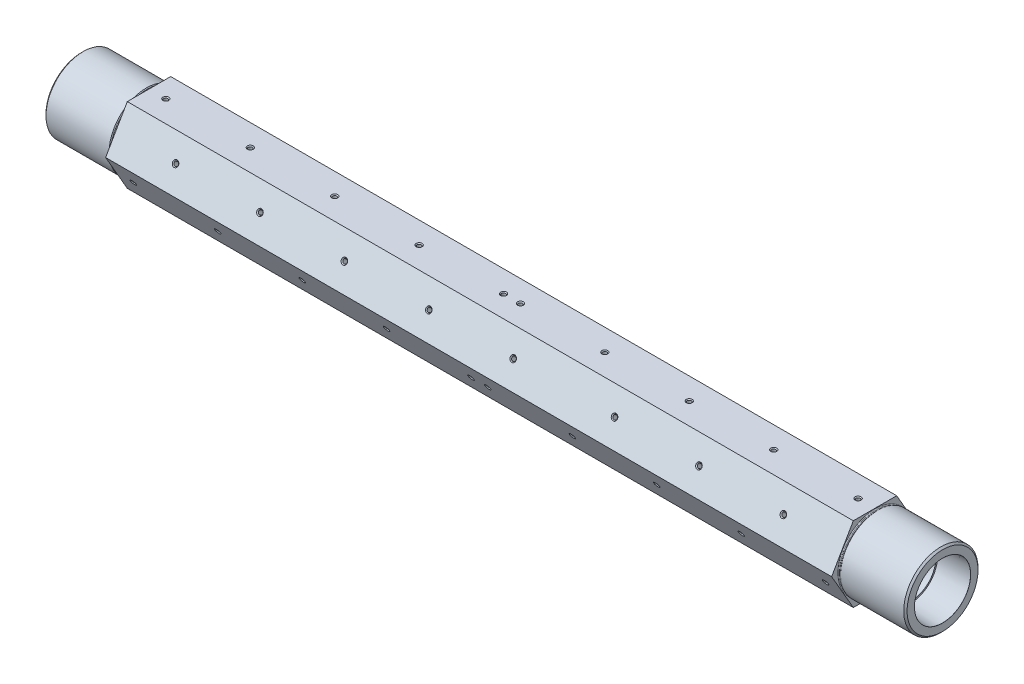
SolidWorks part; units mm, degrees
ref_plane "Спереди" through (0, 0, 0) normal (0, 0, 1) x (1, 0, 0)
ref_plane "Сверху" through (0, 0, 0) normal (0, 1, 0) x (1, 0, 0)
ref_plane "Справа" through (0, 0, 0) normal (1, 0, 0) x (0, 0, -1)
ref_plane "Плоскость4" through (470, 0, 0) normal (1, 0, 0) x (0, 0, -1)
sketch "Эскиз1" plane through (470, 0, 0) normal (1, 0, 0) x (0, 0, -1)
  line L0 (-12.846, -22.25) -> (12.846, -22.25)
  line L1 (12.846, -22.25) -> (25.6921, 0)
  line L2 (25.6921, 0) -> (12.846, 22.25)
  line L3 (12.846, 22.25) -> (-12.846, 22.25)
  line L4 (-12.846, 22.25) -> (-25.6921, 0)
  line L5 (-25.6921, 0) -> (-12.846, -22.25)
extrude "Бобышка-Вытянуть1" add sketch "Эскиз1" against normal blind 430
sketch "Эскиз2" plane through (0, 0, 0) normal (0, 0, 1) x (1, 0, 0)
  line L0 (0, 22) -> (0, 0)
  line L1 (0, 0) -> (40, 0)
  line L2 (40, 0) -> (40, 21.5)
  line L3 (40, 21.5) -> (38.8757, 21.5)
  line L4 (38.8757, 21.5) -> (38.3757, 22)
  line L5 (38.3757, 22) -> (0, 22)
  line L6 (0, 0) -> (40, 0) construction
revolve "Повернуть1" add sketch "Эскиз2" angle 360 about L6
sketch "Эскиз3" plane through (0, 0, 0) normal (0, 0, 1) x (1, 0, 0)
  line L0 (470, 21.5) -> (470, 0)
  line L1 (470, 0) -> (510, 0)
  line L2 (510, 0) -> (510, 22)
  line L3 (510, 22) -> (471.6243, 22)
  line L4 (471.6243, 22) -> (471.1243, 21.5)
  line L5 (471.1243, 21.5) -> (470, 21.5)
  line L6 (470, 0) -> (510, 0) construction
revolve "Повернуть2" add sketch "Эскиз3" angle 360 about L6
sketch "Эскиз4" plane through (0, 0, 0) normal (0, 0, 1) x (1, 0, 0)
  line L0 (0, 16.6253) -> (0, 0)
  line L1 (0, 0) -> (510, 0)
  line L2 (510, 0) -> (510, 16.6253)
  line L3 (510, 16.6253) -> (491, 16.0322)
  line L4 (491, 16.0322) -> (491, 15.1455)
  line L5 (491, 15.1455) -> (474, 15.1455)
  line L6 (474, 15.1455) -> (474, 12)
  line L7 (474, 12) -> (36, 12)
  line L8 (36, 12) -> (36, 15.145)
  line L9 (36, 15.145) -> (19, 15.145)
  line L10 (19, 15.145) -> (19, 16.0322)
  line L11 (19, 16.0322) -> (0, 16.6253)
  line L12 (0, 0) -> (510, 0) construction
revolve "Вырез-Повернуть1" cut sketch "Эскиз4" angle 360 about L12
hole_wizard "Диаметр отверстия Ø2.5 (2.5)1" positions "Эскиз6" profile "Эскиз5" hole size "Ø2.5" standard "Ansi Metric"
sketch "Эскиз6" plane through (0, 11.125, 19.2691) normal (0, 0.5, 0.866) x (1, 0, 0)
  line L0 (470, 12.846) -> (470, -12.846) construction
  point P0 (75, 0)
  point P1 (125, 0)
  point P2 (175, 0)
  point P3 (225, 0)
  point P4 (275, 0)
  point P5 (335, 0)
  point P6 (385, 0)
  point P7 (435, 0)
  dimension "D1" = 35
  dimension "D2" = 50
  dimension "D3" = 60
  dimension "D4" = 50
sketch "Эскиз5" plane through (75, 11.125, 19.2691) normal (1, 0, 0) x (0, -0.866, 0.5)
  line L0 (0, 0) -> (0, 7.7511)
  line L1 (0, 7.7511) -> (1.25, 7)
  line L2 (1.25, 7) -> (1.25, 0)
  line L5 (1.25, 0) -> (0, 0)
  line L10 (0, 7.7511) -> (-1.25, 7) construction
  line L11 (0, -6.35) -> (0, 107.95) construction
  dimension "Диаметр отверстия" = 2.5
  dimension "Глубина отверстия" = 7
  dimension "Угол заточки сверла" = 118
hole_wizard "Диаметр отверстия Ø2.5 (2.5)2" positions "Эскиз8" profile "Эскиз7" hole size "Ø2.5" standard "Ansi Metric"
sketch "Эскиз8" plane through (0, -22.25, 0) normal (0, -1, 0) x (-1, 0, 0)
  line L0 (-470, -12.846) -> (-470, 12.846) construction
  point P0 (-75, 0)
  point P1 (-125, 0)
  point P2 (-175, 0)
  point P3 (-225, 0)
  point P4 (-275, 0)
  point P5 (-335, 0)
  point P6 (-385, 0)
  point P7 (-435, 0)
  dimension "D1" = 35
  dimension "D2" = 50
  dimension "D3" = 50
  dimension "D4" = 60
sketch "Эскиз7" plane through (75, -22.25, 0) normal (1, 0, 0) x (0, 0, -1)
  line L0 (0, 0) -> (0, 7.7511)
  line L1 (0, 7.7511) -> (1.25, 7)
  line L2 (1.25, 7) -> (1.25, 0)
  line L5 (1.25, 0) -> (0, 0)
  line L10 (0, 7.7511) -> (-1.25, 7) construction
  line L11 (0, -6.35) -> (0, 107.95) construction
  dimension "Диаметр отверстия" = 2.5
  dimension "Глубина отверстия" = 7
  dimension "Угол заточки сверла" = 118
hole_wizard "Диаметр отверстия Ø2.5 (2.5)3" positions "Эскиз10" profile "Эскиз9" hole size "Ø2.5" standard "Ansi Metric"
sketch "Эскиз10" plane through (0, -11.125, 19.2691) normal (0, -0.5, 0.866) x (1, 0, 0)
  point P0 (50, 0)
  point P1 (100, 0)
  point P2 (150, 0)
  point P3 (200, 0)
  point P4 (250, 0)
  point P5 (460, 0)
  point P6 (410, 0)
  point P7 (360, 0)
  point P8 (310, 0)
  point P9 (260, 0)
sketch "Эскиз9" plane through (50, -11.125, 19.2691) normal (1, 0, 0) x (0, -0.866, -0.5)
  line L0 (0, 0) -> (0, 7.7511)
  line L1 (0, 7.7511) -> (1.25, 7)
  line L2 (1.25, 7) -> (1.25, 0)
  line L5 (1.25, 0) -> (0, 0)
  line L10 (0, 7.7511) -> (-1.25, 7) construction
  line L11 (0, -6.35) -> (0, 107.95) construction
  dimension "Диаметр отверстия" = 2.5
  dimension "Глубина отверстия" = 7
  dimension "Угол заточки сверла" = 118
hole_wizard "Диаметр отверстия Ø2.5 (2.5)4" positions "Эскиз12" profile "Эскиз11" hole size "Ø2.5" standard "Ansi Metric"
sketch "Эскиз12" plane through (0, -11.125, -19.2691) normal (0, -0.5, -0.866) x (-1, 0, 0)
  point P0 (-50, 0)
  point P1 (-100, 0)
  point P2 (-150, 0)
  point P3 (-200, 0)
  point P4 (-250, 0)
  point P5 (-460, 0)
  point P6 (-410, 0)
  point P7 (-360, 0)
  point P8 (-310, 0)
  point P9 (-260, 0)
sketch "Эскиз11" plane through (50, -11.125, -19.2691) normal (1, 0, 0) x (0, 0.866, -0.5)
  line L0 (0, 0) -> (0, 7.7511)
  line L1 (0, 7.7511) -> (1.25, 7)
  line L2 (1.25, 7) -> (1.25, 0)
  line L5 (1.25, 0) -> (0, 0)
  line L10 (0, 7.7511) -> (-1.25, 7) construction
  line L11 (0, -6.35) -> (0, 107.95) construction
  dimension "Диаметр отверстия" = 2.5
  dimension "Глубина отверстия" = 7
  dimension "Угол заточки сверла" = 118
hole_wizard "Диаметр отверстия Ø2.5 (2.5)5" positions "Эскиз14" profile "Эскиз13" hole size "Ø2.5" standard "Ansi Metric"
sketch "Эскиз14" plane through (0, 22.25, 0) normal (0, 1, 0) x (1, 0, 0)
  point P0 (260, 0)
  point P1 (310, 0)
  point P2 (360, 0)
  point P3 (50, 0)
  point P4 (100, 0)
  point P5 (150, 0)
  point P6 (200, 0)
  point P7 (250, 0)
  point P8 (460, 0)
  point P9 (410, 0)
sketch "Эскиз13" plane through (260, 22.25, 0) normal (1, 0, 0) x (0, 0, 1)
  line L0 (0, 0) -> (0, 7.7511)
  line L1 (0, 7.7511) -> (1.25, 7)
  line L2 (1.25, 7) -> (1.25, 0)
  line L5 (1.25, 0) -> (0, 0)
  line L10 (0, 7.7511) -> (-1.25, 7) construction
  line L11 (0, -6.35) -> (0, 107.95) construction
  dimension "Диаметр отверстия" = 2.5
  dimension "Глубина отверстия" = 7
  dimension "Угол заточки сверла" = 118
hole_wizard "Диаметр отверстия Ø2.5 (2.5)6" positions "Эскиз16" profile "Эскиз15" hole size "Ø2.5" standard "Ansi Metric"
sketch "Эскиз16" plane through (0, 11.125, -19.2691) normal (0, 0.5, -0.866) x (-1, 0, 0)
  line L0 (-470, -12.846) -> (-470, 12.846) construction
  point P0 (-435, 0)
  point P1 (-385, 0)
  point P2 (-335, 0)
  point P3 (-275, 0)
  point P4 (-225, 0)
  point P5 (-175, 0)
  point P6 (-75, 0)
  point P7 (-125, 0)
  dimension "D1" = 35
  dimension "D2" = 50
  dimension "D3" = 50
  dimension "D4" = 60
sketch "Эскиз15" plane through (435, 11.125, -19.2691) normal (1, 0, 0) x (0, 0.866, 0.5)
  line L0 (0, 0) -> (0, 7.7511)
  line L1 (0, 7.7511) -> (1.25, 7)
  line L2 (1.25, 7) -> (1.25, 0)
  line L5 (1.25, 0) -> (0, 0)
  line L10 (0, 7.7511) -> (-1.25, 7) construction
  line L11 (0, -6.35) -> (0, 107.95) construction
  dimension "Диаметр отверстия" = 2.5
  dimension "Глубина отверстия" = 7
  dimension "Угол заточки сверла" = 118
chamfer "Фаска1" distance 0.5 angle 45 54 edges at (360, -12.2075, 18.6441) (335, 10.0425, 19.8941) (275, -22.25, -1.25) (175, 12.2075, -18.6441) (225, 12.2075, -18.6441) (260, 22.25, 1.25) (75, 10.0425, 19.8941) (310, 22.25, 1.25) (125, 10.0425, 19.8941) (360, 22.25, 1.25) (50, 22.25, 1.25) (260, -10.0425, -19.8941) (100, 22.25, 1.25) (260, -12.2075, 18.6441) (150, 22.25, 1.25) (175, -22.25, -1.25) (200, 22.25, 1.25) (385, -22.25, -1.25) (250, 22.25, 1.25) (225, 10.0425, 19.8941) (460, 22.25, 1.25) (435, 10.0425, 19.8941) (410, 22.25, 1.25) (75, 12.2075, -18.6441) (310, -10.0425, -19.8941) (125, 12.2075, -18.6441) (410, -12.2075, 18.6441) (50, -10.0425, -19.8941) (310, -12.2075, 18.6441) (50, -12.2075, 18.6441) (75, -22.25, -1.25) (100, -10.0425, -19.8941) (125, -22.25, -1.25) (150, -10.0425, -19.8941) (225, -22.25, -1.25) (200, -10.0425, -19.8941) (335, -22.25, -1.25) (250, -10.0425, -19.8941) (435, -22.25, -1.25) (100, -12.2075, 18.6441) (175, 10.0425, 19.8941) (150, -12.2075, 18.6441) (275, 10.0425, 19.8941) (200, -12.2075, 18.6441) (385, 10.0425, 19.8941) (250, -12.2075, 18.6441) (460, -10.0425, -19.8941) (385, 12.2075, -18.6441) (275, 12.2075, -18.6441) (335, 12.2075, -18.6441) (360, -10.0425, -19.8941) (460, -12.2075, 18.6441) (435, 12.2075, -18.6441) (410, -10.0425, -19.8941)
chamfer "Фаска2" distance 1 angle 45 2 edges at (510, 0, -22) (0, 0, -22)
chamfer "Фаска3" distance 0.0242 angle 45 2 edges at (510, 0, -16.6253) (0, 0, -16.6253)
fillet "Скругление1" radius 0.3 2 edges at (471.1243, 0, -21.5) (38.8757, 0, -21.5)
fillet "Скругление2" radius 0.5 2 edges at (470, 0, -21.5) (40, 0, -21.5)
